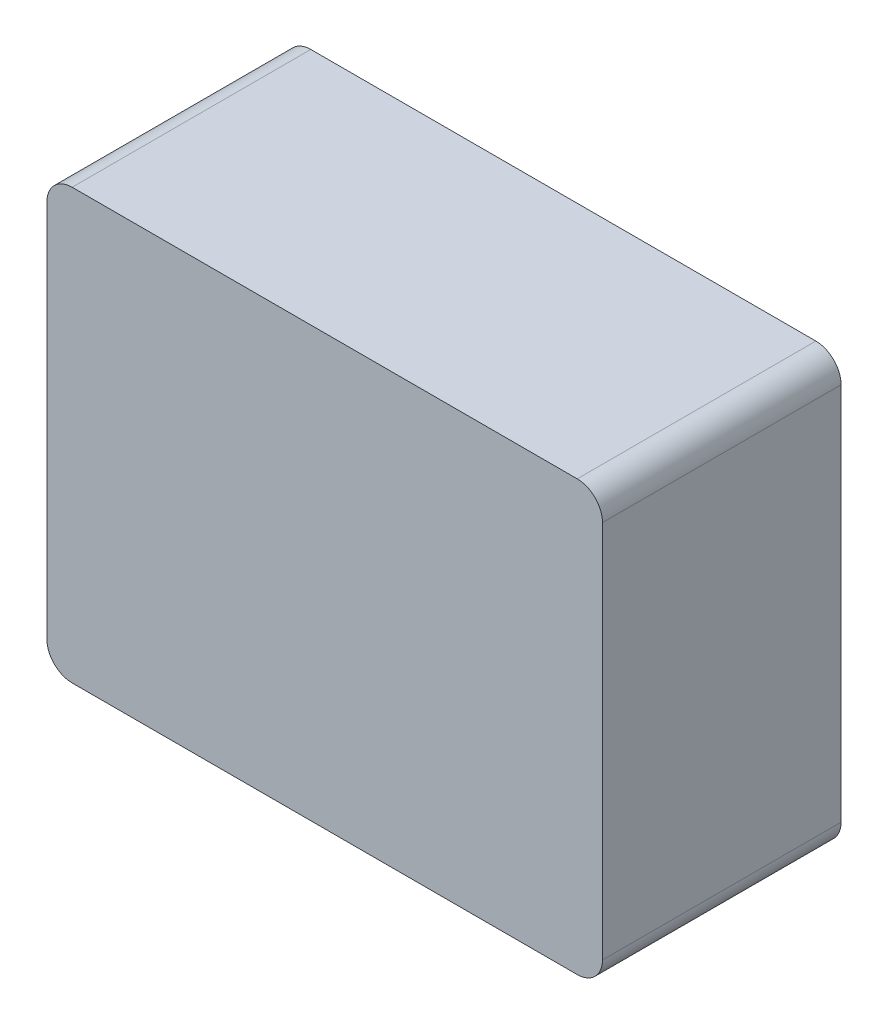
SolidWorks part; units mm, degrees
ref_plane "Front Plane" through (0, 0, 0) normal (0, 0, 1) x (1, 0, 0)
ref_plane "Top Plane" through (0, 0, 0) normal (0, 1, 0) x (1, 0, 0)
ref_plane "Right Plane" through (0, 0, 0) normal (1, 0, 0) x (0, 0, -1)
sketch "Sketch1" plane through (0, 0, 0) normal (0, 1, 0) x (1, 0, 0)
  line L1 (0, 0) -> (44, 0)
  line L2 (0, 0) -> (0, 18.9)
  line L3 (0, 18.9) -> (44, 18.9)
  line L4 (44, 0) -> (44, 18.9)
  dimension "D1" = 18.9
  dimension "D2" = 44
extrude "Boss-Extrude1" add sketch "Sketch1" along normal blind 34 contours L3 L4 L1 L2
fillet "Fillet1" radius 2 4 edges at (0, 0, -9.45) (44, 0, -9.45) (44, 34, -9.45) (0, 34, -9.45)
sketch "Sketch2" plane through (0, 0, 0) normal (0, -1, 0) x (-1, 0, 0)
  line L0 (-11, 3.02) -> (-33, 3.02) construction
  line L1 (-33, 3.02) -> (-33, 15.02) construction
  line L2 (-33, 15.02) -> (-11, 15.02) construction
  line L3 (-11, 15.02) -> (-11, 3.02) construction
  line L4 (-11, 9.02) -> (-2, 9.02) construction
  line L6 (-33, 9.02) -> (-42, 9.02) construction
  line L8 (-2, 18.9) -> (-42, 18.9) construction
  line L9 (-2, 0) -> (-2, 18.9) construction
  line L10 (-42, 18.9) -> (-42, 0) construction
  circle A0 centre (-11, 3.02) radius 1
  circle A1 centre (-33, 3.02) radius 1
  circle A2 centre (-11, 15.02) radius 1
  circle A3 centre (-33, 15.02) radius 1
  dimension "D4" = 2
  dimension "D1" = 12
  dimension "D2" = 22
  dimension "D3" = 3.88
extrude "Cut-Extrude1" cut sketch "Sketch2" against normal blind 3.5
sketch "Sketch3" plane through (0, 0, 0) normal (0, 0, 1) x (1, 0, 0)
  line L0 (0, 17) -> (22, 17) construction
  line L1 (0, 32) -> (0, 2) construction
  line L2 (22, 17) -> (44, 17) construction
  line L3 (44, 32) -> (44, 2) construction
  line L4 (22, 17) -> (22, 34) construction
  line L5 (2, 34) -> (42, 34) construction
  line L6 (22, 17) -> (22, 0) construction
  line L7 (2, 0) -> (42, 0) construction
  circle A0 centre (22, 17) radius 15
  dimension "D1" = 30
